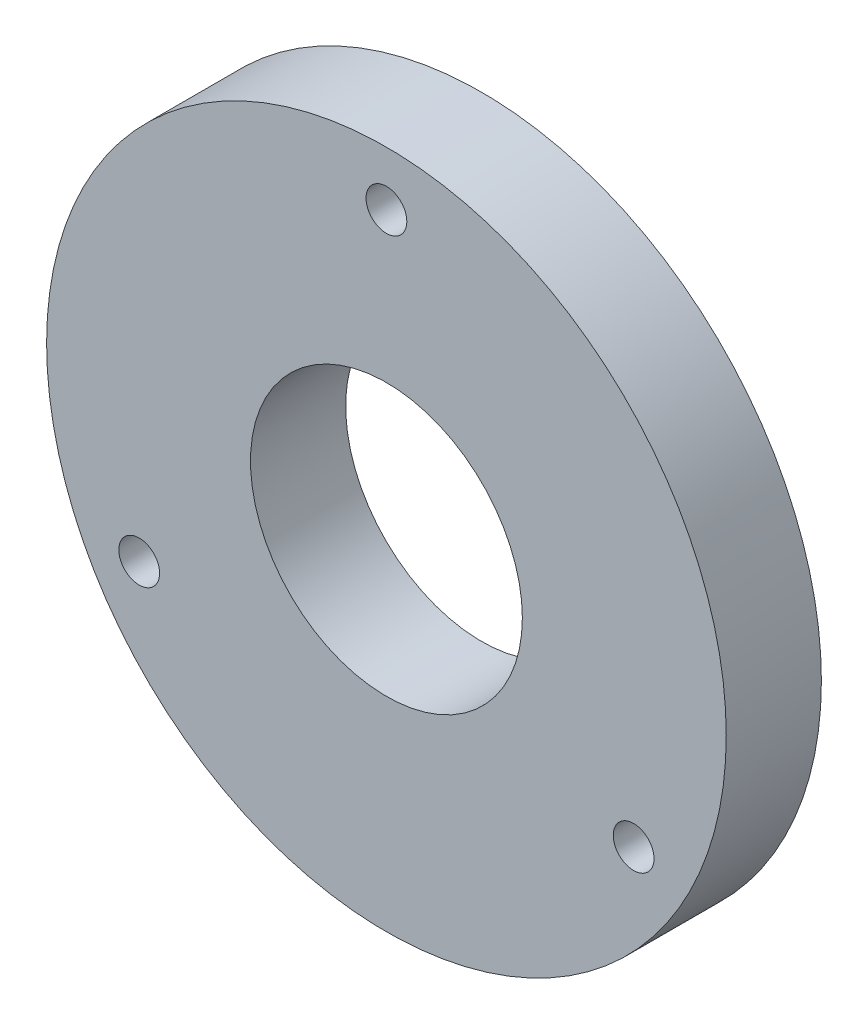
SolidWorks part; units mm, degrees
ref_plane "Front Plane" through (0, 0, 0) normal (0, 0, 1) x (1, 0, 0)
ref_plane "Top Plane" through (0, 0, 0) normal (0, 1, 0) x (1, 0, 0)
ref_plane "Right Plane" through (0, 0, 0) normal (1, 0, 0) x (0, 0, -1)
sketch "Sketch1" plane through (0, 0, 0) normal (0, 0, 1) x (1, 0, 0)
  circle A0 centre (0, 0) radius 25
  circle A1 centre (0, 0) radius 10
  dimension "D1" = 50
  dimension "D2" = 20
extrude "Boss-Extrude2" add sketch "Sketch1" along normal blind 7
hole_wizard "Ø3.0mm Dowel Hole1" positions "Sketch3" profile "Sketch4" hole size "Ø3.0" standard "ANSI Metric" end condition through all
sketch "Sketch3" plane through (0, 0, 7) normal (0, 0, 1) x (1, 0, 0)
  point P0 (0, 21)
  dimension "D1" = 21
sketch "Sketch4" plane through (0, 21, 7) normal (1, 0, 0) x (0, -1, 0)
  line L0 (0, 0) -> (0, 7)
  line L1 (0, 7) -> (1.5, 7)
  line L2 (1.5, 7) -> (1.5, 0)
  line L5 (1.5, 0) -> (0, 0)
  line L11 (0, -6.35) -> (0, 107.95) construction
  dimension "Thru Hole Dia." = 3
  dimension "Thru Hole Depth" = 7
pattern_circular "CirPattern1" count 3 over 360 about axis through (0, 0, 0) along (0, 0, 1) of "Ø3.0mm Dowel Hole1"
